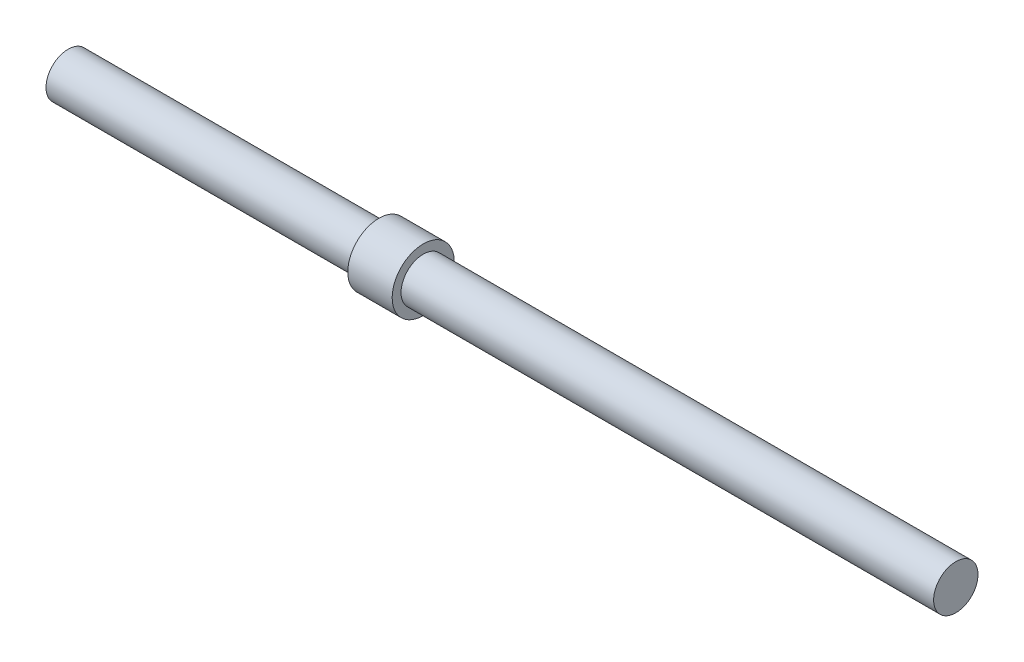
SolidWorks part; units mm, degrees
ref_plane "Front Plane" through (0, 0, 0) normal (0, 0, 1) x (1, 0, 0)
ref_plane "Top Plane" through (0, 0, 0) normal (0, 1, 0) x (1, 0, 0)
ref_plane "Right Plane" through (0, 0, 0) normal (1, 0, 0) x (0, 0, -1)
sketch "Sketch1" plane through (0, 0, 0) normal (1, 0, 0) x (0, 0, -1)
  circle A0 centre (0, 0) radius 5
  dimension "D1" = 10
extrude "Boss-Extrude1" add sketch "Sketch1" along normal mid plane 200
sketch "Sketch2" plane through (-100, 0, 0) normal (-1, 0, 0) x (0, 0, 1)
  circle A0 centre (0, 0) radius 7
  dimension "D1" = 14
extrude "Boss-Extrude2" add sketch "Sketch2" against normal blind 10 from offset 70 offset against normal yes
